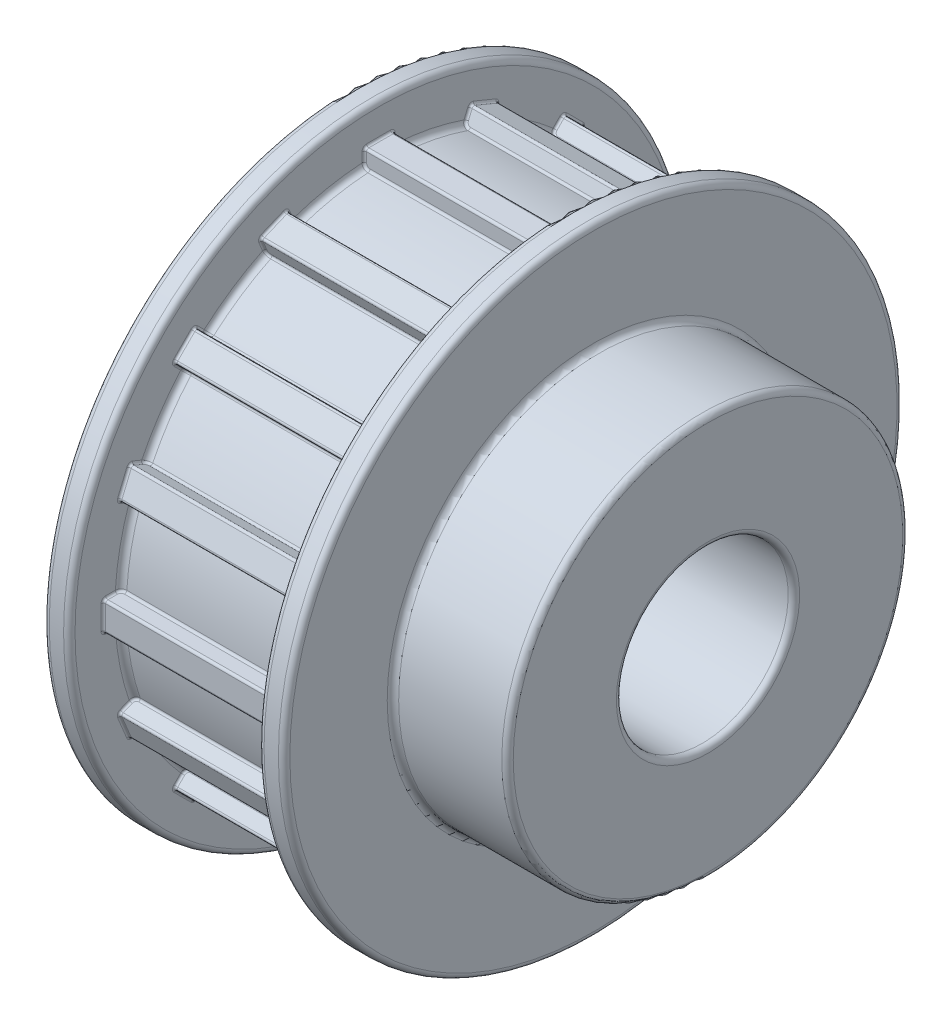
SolidWorks part; units mm, degrees
ref_plane "Front Plane" through (0, 0, 0) normal (0, 0, 1) x (1, 0, 0)
ref_plane "Top Plane" through (0, 0, 0) normal (0, 1, 0) x (1, 0, 0)
ref_plane "Right Plane" through (0, 0, 0) normal (1, 0, 0) x (0, 0, -1)
sketch "Sketch1" plane through (0, 0, 0) normal (0, 0, 1) x (1, 0, 0)
  line L0 (0, 7.5) -> (31, 7.5)
  line L1 (31, 7.5) -> (31, 17.5)
  line L2 (31, 17.5) -> (21, 17.5)
  line L3 (21, 17.5) -> (21, 27)
  line L4 (21, 27) -> (18.75, 27)
  line L5 (0, 27) -> (0, 7.5)
  line L6 (-1179.0887, 0) -> (57775.3476, 0) construction
  line L7 (18.75, 27) -> (18.75, 22.525)
  line L8 (18.75, 22.525) -> (2.25, 22.525)
  line L9 (2.25, 22.525) -> (2.25, 27)
  line L10 (2.25, 27) -> (0, 27)
  dimension "D1" = 7.5
  dimension "D2" = 31
  dimension "D3" = 21
  dimension "D4" = 27
  dimension "D5" = 17.5
  dimension "D6" = 2.25
  dimension "D7" = 2.25
  dimension "D8" = 22.525
revolve "Revolve1" add sketch "Sketch1" angle 360 about L6
fillet "Fillet1" radius 0.5 10 edges at (21, 0, 27) (0, 0, 7.5) (31, 0, 7.5) (21, 0, 17.5) (31, 0, 17.5) (0, 0, 27) (2.25, 0, 27) (2.25, 0, 22.525) (18.75, 0, 22.525) (18.75, 0, 27)
ref_plane "Plane1" through (2.25, 0, 0) normal (-1, 0, 0) x (0, 0, 1)
sketch "Sketch3" plane through (2.25, 0, 0) normal (-1, 0, 0) x (0, 0, 1)
  line L0 (10.3488, 21.7179) -> (8.0391, 22.6746)
  line L1 (1.25, 21.025) -> (-1.25, 21.025)
  line L2 (1.25, 21.025) -> (1.25, 24.025)
  line L3 (1.25, 24.025) -> (-1.25, 24.025)
  line L4 (-1.25, 21.025) -> (-1.25, 24.025)
  line L5 (1.25, 21.025) -> (-1.25, 24.025) construction
  line L6 (1.25, 24.025) -> (-1.25, 21.025) construction
  line L7 (9.2008, 18.9462) -> (10.3488, 21.7179)
  line L8 (9.2008, 18.9462) -> (6.8911, 19.9029)
  line L9 (6.8911, 19.9029) -> (8.0391, 22.6746)
  line L10 (9.2008, 18.9462) -> (8.0391, 22.6746) construction
  line L11 (10.3488, 21.7179) -> (6.8911, 19.9029) construction
  line L12 (17.8721, 16.1044) -> (16.1044, 17.8721)
  line L13 (15.7508, 13.983) -> (17.8721, 16.1044)
  line L14 (15.7508, 13.983) -> (13.983, 15.7508)
  line L15 (13.983, 15.7508) -> (16.1044, 17.8721)
  line L16 (15.7508, 13.983) -> (16.1044, 17.8721) construction
  line L17 (17.8721, 16.1044) -> (13.983, 15.7508) construction
  line L18 (22.6746, 8.0391) -> (21.7179, 10.3488)
  line L19 (19.9029, 6.8911) -> (22.6746, 8.0391)
  line L20 (19.9029, 6.8911) -> (18.9462, 9.2008)
  line L21 (18.9462, 9.2008) -> (21.7179, 10.3488)
  line L22 (19.9029, 6.8911) -> (21.7179, 10.3488) construction
  line L23 (22.6746, 8.0391) -> (18.9462, 9.2008) construction
  line L24 (24.025, -1.25) -> (24.025, 1.25)
  line L25 (21.025, -1.25) -> (24.025, -1.25)
  line L26 (21.025, -1.25) -> (21.025, 1.25)
  line L27 (21.025, 1.25) -> (24.025, 1.25)
  line L28 (21.025, -1.25) -> (24.025, 1.25) construction
  line L29 (24.025, -1.25) -> (21.025, 1.25) construction
  line L30 (21.7179, -10.3488) -> (22.6746, -8.0391)
  line L31 (18.9462, -9.2008) -> (21.7179, -10.3488)
  line L32 (18.9462, -9.2008) -> (19.9029, -6.8911)
  line L33 (19.9029, -6.8911) -> (22.6746, -8.0391)
  line L34 (18.9462, -9.2008) -> (22.6746, -8.0391) construction
  line L35 (21.7179, -10.3488) -> (19.9029, -6.8911) construction
  line L36 (16.1044, -17.8721) -> (17.8721, -16.1044)
  line L37 (13.983, -15.7508) -> (16.1044, -17.8721)
  line L38 (13.983, -15.7508) -> (15.7508, -13.983)
  line L39 (15.7508, -13.983) -> (17.8721, -16.1044)
  line L40 (13.983, -15.7508) -> (17.8721, -16.1044) construction
  line L41 (16.1044, -17.8721) -> (15.7508, -13.983) construction
  line L42 (8.0391, -22.6746) -> (10.3488, -21.7179)
  line L43 (6.8911, -19.9029) -> (8.0391, -22.6746)
  line L44 (6.8911, -19.9029) -> (9.2008, -18.9462)
  line L45 (9.2008, -18.9462) -> (10.3488, -21.7179)
  line L46 (6.8911, -19.9029) -> (10.3488, -21.7179) construction
  line L47 (8.0391, -22.6746) -> (9.2008, -18.9462) construction
  line L48 (-1.25, -24.025) -> (1.25, -24.025)
  line L49 (-1.25, -21.025) -> (-1.25, -24.025)
  line L50 (-1.25, -21.025) -> (1.25, -21.025)
  line L51 (1.25, -21.025) -> (1.25, -24.025)
  line L52 (-1.25, -21.025) -> (1.25, -24.025) construction
  line L53 (-1.25, -24.025) -> (1.25, -21.025) construction
  line L54 (-10.3488, -21.7179) -> (-8.0391, -22.6746)
  line L55 (-9.2008, -18.9462) -> (-10.3488, -21.7179)
  line L56 (-9.2008, -18.9462) -> (-6.8911, -19.9029)
  line L57 (-6.8911, -19.9029) -> (-8.0391, -22.6746)
  line L58 (-9.2008, -18.9462) -> (-8.0391, -22.6746) construction
  line L59 (-10.3488, -21.7179) -> (-6.8911, -19.9029) construction
  line L60 (-17.8721, -16.1044) -> (-16.1044, -17.8721)
  line L61 (-15.7508, -13.983) -> (-17.8721, -16.1044)
  line L62 (-15.7508, -13.983) -> (-13.983, -15.7508)
  line L63 (-13.983, -15.7508) -> (-16.1044, -17.8721)
  line L64 (-15.7508, -13.983) -> (-16.1044, -17.8721) construction
  line L65 (-17.8721, -16.1044) -> (-13.983, -15.7508) construction
  line L66 (-22.6746, -8.0391) -> (-21.7179, -10.3488)
  line L67 (-19.9029, -6.8911) -> (-22.6746, -8.0391)
  line L68 (-19.9029, -6.8911) -> (-18.9462, -9.2008)
  line L69 (-18.9462, -9.2008) -> (-21.7179, -10.3488)
  line L70 (-19.9029, -6.8911) -> (-21.7179, -10.3488) construction
  line L71 (-22.6746, -8.0391) -> (-18.9462, -9.2008) construction
  line L72 (-24.025, 1.25) -> (-24.025, -1.25)
  line L73 (-21.025, 1.25) -> (-24.025, 1.25)
  line L74 (-21.025, 1.25) -> (-21.025, -1.25)
  line L75 (-21.025, -1.25) -> (-24.025, -1.25)
  line L76 (-21.025, 1.25) -> (-24.025, -1.25) construction
  line L77 (-24.025, 1.25) -> (-21.025, -1.25) construction
  line L78 (-21.7179, 10.3488) -> (-22.6746, 8.0391)
  line L79 (-18.9462, 9.2008) -> (-21.7179, 10.3488)
  line L80 (-18.9462, 9.2008) -> (-19.9029, 6.8911)
  line L81 (-19.9029, 6.8911) -> (-22.6746, 8.0391)
  line L82 (-18.9462, 9.2008) -> (-22.6746, 8.0391) construction
  line L83 (-21.7179, 10.3488) -> (-19.9029, 6.8911) construction
  line L84 (-16.1044, 17.8721) -> (-17.8721, 16.1044)
  line L85 (-13.983, 15.7508) -> (-16.1044, 17.8721)
  line L86 (-13.983, 15.7508) -> (-15.7508, 13.983)
  line L87 (-15.7508, 13.983) -> (-17.8721, 16.1044)
  line L88 (-13.983, 15.7508) -> (-17.8721, 16.1044) construction
  line L89 (-16.1044, 17.8721) -> (-15.7508, 13.983) construction
  line L90 (-8.0391, 22.6746) -> (-10.3488, 21.7179)
  line L91 (-6.8911, 19.9029) -> (-8.0391, 22.6746)
  line L92 (-6.8911, 19.9029) -> (-9.2008, 18.9462)
  line L93 (-9.2008, 18.9462) -> (-10.3488, 21.7179)
  line L94 (-6.8911, 19.9029) -> (-10.3488, 21.7179) construction
  line L95 (-8.0391, 22.6746) -> (-9.2008, 18.9462) construction
  circle A0 centre (0, 0) radius 7.5 construction
  circle A1 centre (0, 0) radius 26.5
  circle A2 centre (0, 0) radius 26.5
  circle A3 centre (0, 0) radius 7.5
  circle A4 centre (0, 0) radius 7.5
  circle A5 centre (0, 0) radius 7.5
  circle A6 centre (0, 0) radius 7.5
  circle A7 centre (0, 0) radius 7.5
  circle A8 centre (0, 0) radius 7.5
  circle A9 centre (0, 0) radius 7.5
  circle A10 centre (0, 0) radius 7.5
  circle A11 centre (0, 0) radius 7.5
  circle A12 centre (0, 0) radius 7.5
  circle A13 centre (0, 0) radius 7.5
  circle A14 centre (0, 0) radius 7.5
  circle A15 centre (0, 0) radius 7.5
  circle A16 centre (0, 0) radius 7.5
  circle A17 centre (0, 0) radius 7.5
  circle A18 centre (0, 0) radius 7.5
  point P0 (0, 22.525)
  point P88 (0, 0)
  dimension "D1" = 22.525
  dimension "D2" = 2.5
  dimension "D3" = 1.5
  dimension "D4" = 0
  dimension "D5" = 16
extrude "Boss-Extrude2" add sketch "Sketch3" against normal blind 16.5 contours L93 L92 L91 L90 | L4 L1 L2 L3 | L9 L8 L7 L0 | L15 L14 L13 L12 | L21 L20 L19 L18 | L33 L32 L31 L30 | L39 L38 L37 L36 | L45 L44 L43 L42 | L51 L50 L49 L48 | L57 L56 L55 L54 | L63 L62 L61 L60 | L69 L68 L67 L66 | L75 L74 L73 L72 | L87 L86 L85 L84 | L81 L80 L79 L78 | L25 L24 L27 L26
fillet "Fillet2" radius 0.2 70 edges at (2.4382, 9.8033, -20.401) (18.6018, 7.5073, -21.3906) (2.25, 7.8413, -22.1969) (2.25, 1.25, -23.508) (18.6018, -7.5073, -21.3906) (2.25, -7.8413, -22.1969) (18.6018, -9.817, -20.4339) (18.6018, -15.1216, -16.8894) (2.25, -15.7388, -17.5066) (2.4382, -15.0965, -16.8642) (18.6018, -16.8894, -15.1216) (2.25, -17.5066, -15.7388) (18.75, -21.2402, -10.151) (2.25, -21.2402, -10.151) (2.4382, -20.401, -9.8033) (2.25, -23.508, -1.25) (2.25, -23.508, 1.25) (2.4382, -20.401, 9.8033) (18.75, -17.5066, 15.7388) (18.6018, -15.1216, 16.8894) (18.75, -10.151, 21.2402) (18.75, -1.25, 23.508) (3.0955, 1.25, 23.353) (18.75, 10.151, 21.2402) (18.6018, 9.817, 20.4339) (2.25, 7.8413, 22.1969) (2.4382, 7.4936, 21.3577) (18.6018, 15.1216, 16.8894) (2.25, 17.5066, 15.7388) (2.25, 22.1969, 7.8413) (2.4382, 21.3577, 7.4936) (2.25, 23.508, -1.25) (18.75, 22.1969, -7.8413) (2.25, 22.1969, -7.8413) (2.4382, 21.3577, -7.4936) (2.4382, 20.401, -9.8033) (18.75, 17.5066, -15.7388) (2.25, 17.5066, -15.7388) (2.4382, 16.8642, -15.0965) (10.5, 9.7615, -20.3) (10.5, 1.25, -22.4903) (10.5, -7.4518, -21.2567) (10.5, -15.0192, -16.7869) (10.5, -21.2567, -7.4518) (10.5, -20.3, 9.7615) (10.5, -15.0192, 16.7869) (10.5, -7.4518, 21.2567) (10.5, 9.7615, 20.3) (10.5, 22.4903, 1.25) (10.5, 22.4903, -1.25) (10.5, 15.0192, -16.7869) (2.25, -16.9882, -16.9882) (10.5, -17.8721, -16.1044) (18.75, 9.194, -22.1962) (18.75, 0, -24.025) (18.75, -9.194, -22.1962) (18.75, -22.1962, 9.194) (18.75, -16.9882, 16.9882) (2.25, -9.194, 22.1962) (18.75, 16.9882, 16.9882) (18.75, 22.1962, -9.194) (2.25, 22.1962, -9.194) (2.25, 16.9882, -16.9882) (10.5, 10.3488, -21.7179) (10.5, 21.7179, -10.3488) (10.5, 24.025, 1.25) (10.5, 16.1044, 17.8721) (10.5, -10.3488, 21.7179) (10.5, -17.8721, 16.1044) (10.5, -16.1044, 17.8721)
